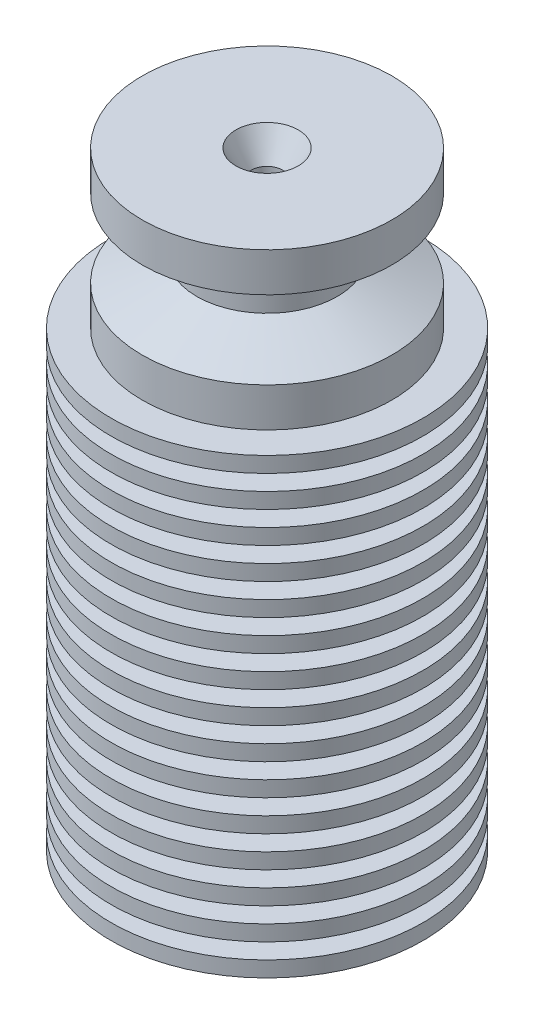
SolidWorks part; units mm, degrees
material "Cuivre"
ref_plane "Plan de face" through (0, 0, 0) normal (0, 0, 1) x (1, 0, 0)
ref_plane "Plan de dessus" through (0, 0, 0) normal (0, 1, 0) x (1, 0, 0)
ref_plane "Plan de droite" through (0, 0, 0) normal (1, 0, 0) x (0, 0, -1)
sketch "Esquisse2" plane through (0, 0, 0) normal (0, 0, 1) x (1, 0, 0)
  line L0 (-1, 0) -> (-1, -44)
  line L1 (-1, -44) -> (-3, -44)
  line L2 (-3, -44) -> (-3, -40)
  line L3 (-3, -40) -> (-2, -40)
  line L4 (-2, -40) -> (-2, -10)
  line L5 (-2, -10) -> (-8, -10)
  line L6 (-8, -10) -> (-8, -7.5)
  line L7 (-8, -7.5) -> (-4.5, -6)
  line L8 (-4.5, -6) -> (-4.5, -4)
  line L9 (-4.5, -4) -> (-8, -2.5)
  line L10 (-8, -2.5) -> (-8, 0)
  line L11 (-8, 0) -> (-1, 0)
  line L12 (0, 9.1912) -> (0, -49.7372) construction
  dimension "D1" = 16
  dimension "D2" = 10
  dimension "D3" = 34
  dimension "D4" = 4
  dimension "D5" = 2
  dimension "D7" = 6
  dimension "D8" = 4
  dimension "D10" = 2.5
  dimension "D11" = 5
  dimension "D12" = 2
  dimension "D13" = 3.5
revolve "Révolution1" add sketch "Esquisse2" angle 360 about L12
cosmetic thread "Représentation de filetage1" parameters "D2"=4.891
sketch "Esquisse3" plane through (0, -10, 0) normal (0, -1, 0) x (1, 0, 0)
  circle A0 centre (0, 0) radius 2
  circle A1 centre (0, 0) radius 10
  circle A2 centre (0, 0) radius 2 construction
  dimension "D1" = 20
extrude "Boss.-Extru.1" add sketch "Esquisse3" along normal blind 1
pattern_linear "Répétition linéaire1" count 15 spacing 2 along (0, -1, 0) of "Boss.-Extru.1"
chamfer "Chanfrein1" distance 1 angle 60 1 edges at (0, 0, 1)
chamfer "Chanfrein3" distance 0.5 angle 45 2 edges at (0, -40, 3) (0, -44, 3)
